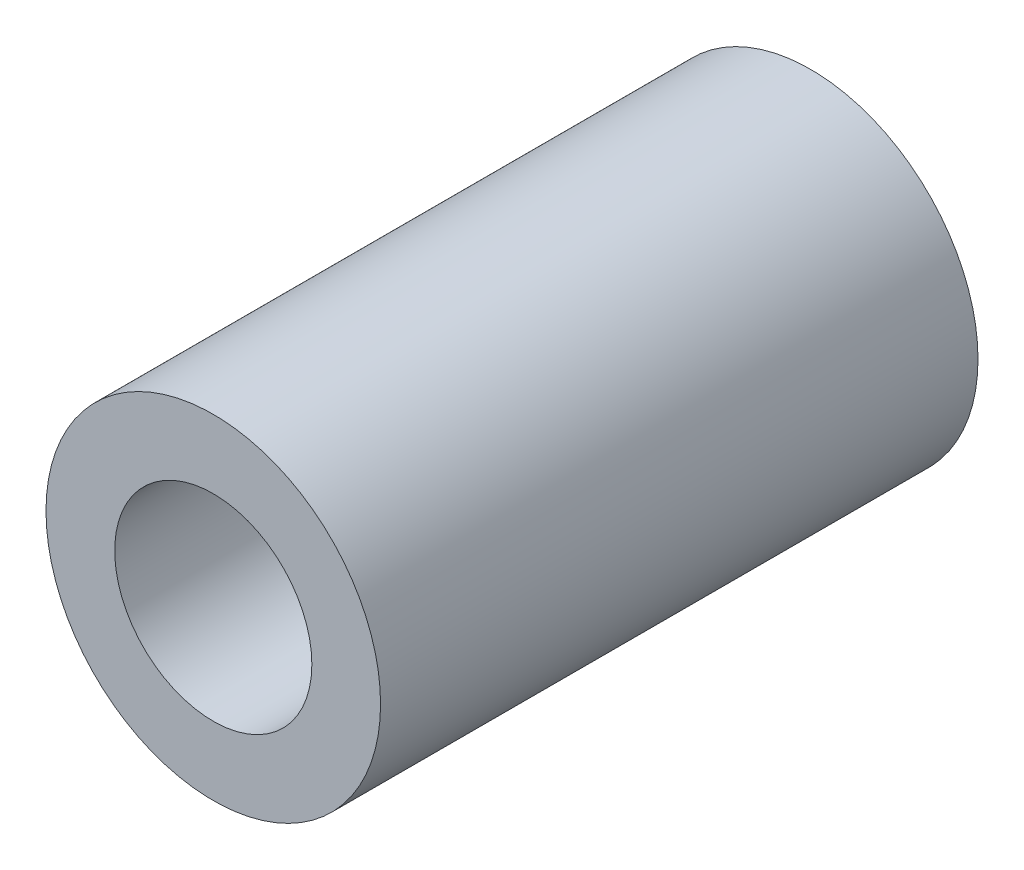
SolidWorks part; units mm, degrees
ref_plane "Front Plane" through (0, 0, 0) normal (0, 0, 1) x (1, 0, 0)
ref_plane "Top Plane" through (0, 0, 0) normal (0, 1, 0) x (1, 0, 0)
ref_plane "Right Plane" through (0, 0, 0) normal (1, 0, 0) x (0, 0, -1)
sketch "Sketch1" plane through (0, 0, 0) normal (0, 0, 1) x (1, 0, 0)
  circle A0 centre (0, 0) radius 2.8
  dimension "D1" = 5.6
extrude "Boss-Extrude1" add sketch "Sketch1" along normal blind 10
sketch "Sketch2" plane through (0, 0, 0) normal (0, 0, 1) x (1, 0, 0)
  circle A0 centre (0, 0) radius 1.65
  dimension "D1" = 3.3
extrude "Cut-Extrude1" cut sketch "Sketch2" along normal blind 10.8208
